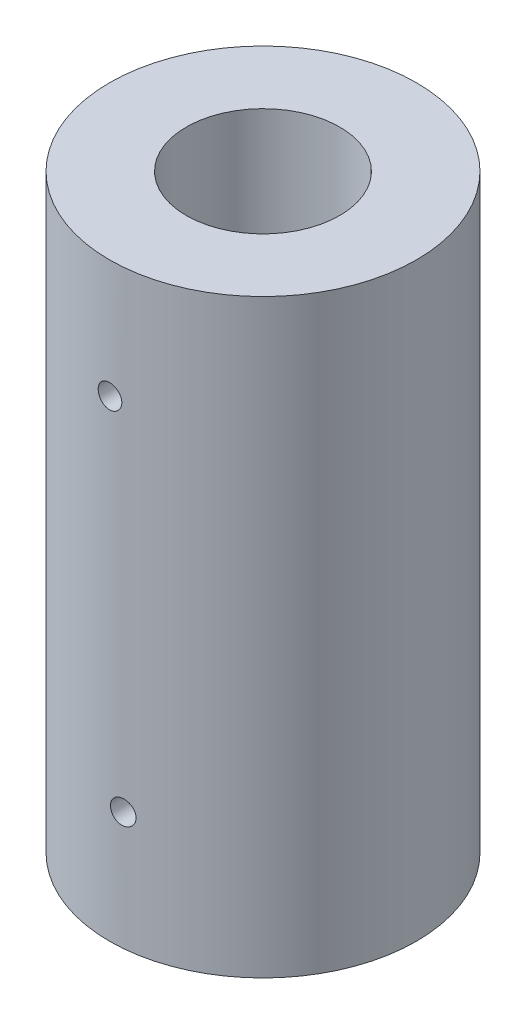
SolidWorks part; units mm, degrees
ref_plane "Front Plane" through (0, 0, 0) normal (0, 0, 1) x (1, 0, 0)
ref_plane "Top Plane" through (0, 0, 0) normal (0, 1, 0) x (1, 0, 0)
ref_plane "Right Plane" through (0, 0, 0) normal (1, 0, 0) x (0, 0, -1)
sketch "Sketch1" plane through (0, 0, 0) normal (0, 1, 0) x (1, 0, 0)
  circle A0 centre (0, 0) radius 6.5
  circle A1 centre (0, 0) radius 13
extrude "Boss-Extrude1" add sketch "Sketch1" along normal blind 50
sketch "Sketch2" plane through (0, 50, 0) normal (0, 1, 0) x (1, 0, 0)
  line L0 (0, 0) -> (0, -13) construction
  circle A0 centre (0, 0) radius 13 construction
ref_plane "Plane1" through (0, 50, 13) normal (0, 0, 1) x (1, 0, 0)
sketch "Sketch3" plane through (0, 50, 13) normal (0, 0, 1) x (1, 0, 0)
  line L0 (-13, -50) -> (13, -50) construction
  circle A0 centre (0, -10) radius 1
  circle A1 centre (1.0777, -40) radius 1
  dimension "D1" = 10
  dimension "D2" = 10
extrude "Cut-Extrude1" cut sketch "Sketch3" against normal blind 73
